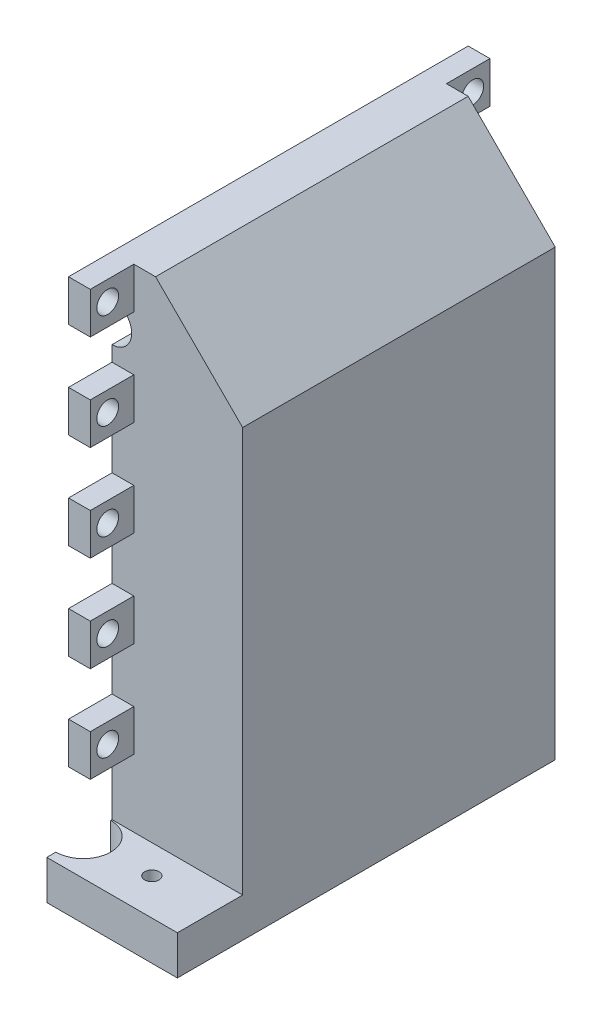
SolidWorks part; units mm, degrees
material "ABS"
ref_plane "Front Plane" through (0, 0, 0) normal (0, 0, 1) x (1, 0, 0)
ref_plane "Top Plane" through (0, 0, 0) normal (0, 1, 0) x (1, 0, 0)
ref_plane "Right Plane" through (0, 0, 0) normal (1, 0, 0) x (0, 0, -1)
sketch "Sketch1" plane through (0, 0, 0) normal (0, 1, 0) x (1, 0, 0)
  line L0 (0, 0) -> (14.605, 0)
  line L1 (21.08, 8.638) -> (48.0208, -18.3028) construction
  line L2 (29.718, 15.113) -> (29.718, 44.323)
  line L3 (21.08, 50.798) -> (48.0208, 77.7388) construction
  line L4 (14.605, 59.436) -> (0, 59.436)
  line L5 (0, 0) -> (0, -25.4)
  line L6 (0, -25.4) -> (38.1, -25.4)
  line L7 (38.1, -25.4) -> (38.1, 84.836)
  line L8 (38.1, 84.836) -> (0, 84.836)
  line L9 (0, 84.836) -> (0, 59.436)
  line L10 (0, 59.436) -> (0.0016, 59.4863)
  arc A0 (14.605, 59.436) -> (29.718, 44.323) centre (48.0208, 77.7388) ccw
  arc A1 (14.605, 0) -> (29.718, 15.113) centre (48.0208, -18.3028) cw
  circle A2 centre (23.622, 6.096) radius 2.54
  circle A3 centre (23.622, 53.34) radius 2.54
  dimension "D9" = 38.1
  dimension "D6" = 38.1
  dimension "D4" = 5.08
  dimension "D11" = 5.08
  dimension "D1" = 29.718
  dimension "D2" = 59.436
  dimension "D3" = 14.605
  dimension "D5" = 29.21
  dimension "D7" = 38.1
  dimension "D8" = 25.4
  dimension "D10" = 25.4
  dimension "D12" = 47.244
extrude "Boss-Extrude1" add sketch "Sketch1" along normal blind 11.43
sketch "Sketch2" plane through (0, 11.43, 0) normal (0, 1, 0) x (1, 0, 0)
  line L0 (38.1, 84.836) -> (0, 84.836) construction
  line L2 (38.1, 84.836) -> (29.718, 84.836)
  line L3 (29.718, 0) -> (29.718, 84.836)
  line L4 (29.718, 15.113) -> (29.718, 44.323) construction
  line L12 (38.1, 84.836) -> (0, 84.836)
  line L13 (0, 84.836) -> (0, 59.436)
  line L14 (0, 59.436) -> (14.605, 59.436)
  line L16 (29.718, 44.323) -> (29.718, 15.113)
  line L18 (14.605, 0) -> (0, 0)
  line L19 (0, 0) -> (0, -25.4)
  line L20 (0, -25.4) -> (38.1, -25.4)
  line L21 (38.1, -25.4) -> (38.1, 84.836)
  line L28 (29.718, 0) -> (0, 0)
  line L29 (0, 0) -> (0, -6.35)
  line L30 (0, -6.35) -> (38.1, -6.35)
  line L31 (38.1, -6.35) -> (38.1, 84.836)
  arc A1 (14.605, 59.436) -> (29.718, 44.323) centre (48.0208, 77.7388) ccw
  arc A3 (29.718, 15.113) -> (14.605, 0) centre (48.0208, -18.3028) ccw
  dimension "D2" = 6.35
  dimension "D1" = 0
extrude "Boss-Extrude2" add sketch "Sketch2" along normal blind 107.95
sketch "Sketch3" plane through (0, 119.38, 0) normal (0, 1, 0) x (1, 0, 0)
  line L0 (38.1, -6.35) -> (38.1, 84.836) construction
  line L1 (0, -6.35) -> (38.1, -6.35)
  line L2 (0, -6.35) -> (0, 84.836)
  line L3 (0, 84.836) -> (38.1, 84.836)
  line L4 (38.1, -6.35) -> (38.1, 84.836)
  line L5 (29.718, 84.836) -> (0, 84.836) construction
  line L6 (0, -6.35) -> (38.1, -6.35) construction
  line L7 (0, 0) -> (0, -6.35) construction
extrude "Boss-Extrude3" add sketch "Sketch3" along normal blind 35.56
sketch "Sketch4" plane through (0, 0, 6.35) normal (0, 0, 1) x (1, 0, 0)
  line L0 (0, 11.43) -> (0, 0) construction
  line L1 (0, 154.94) -> (38.1, 154.94) construction
  circle A0 centre (0, 137.16) radius 5.715
  dimension "D1" = 11.43
  dimension "D2" = 17.78
extrude "Cut-Extrude1" cut sketch "Sketch4" against normal up to next
mirror "Mirror2" [suppressed]
sketch "Sketch5" plane through (0, 0, 6.35) normal (0, 0, 1) x (1, 0, 0)
  line L0 (0, 11.43) -> (0, 0) construction
  line L1 (0, 142.875) -> (6.35, 142.875)
  line L2 (0, 142.875) -> (0, 154.94)
  line L3 (0, 154.94) -> (6.35, 154.94)
  line L4 (6.35, 142.875) -> (6.35, 154.94)
  line L6 (0, 154.94) -> (38.1, 154.94) construction
  dimension "D3" = 6.35
extrude "Boss-Extrude4" add sketch "Sketch5" along normal blind 12.7
hole_wizard "1/4 (0.25) Diameter Hole2" positions "Sketch9" profile "Sketch10" hole size "1/4" standard "ANSI Inch" end condition up to next
sketch "Sketch9" plane through (6.35, 0, 0) normal (1, 0, 0) x (0, 0, -1)
  line L1 (-19.05, 154.94) -> (-6.35, 154.94) construction
  line L2 (-19.05, 142.875) -> (-19.05, 154.94) construction
  point P0 (-13.97, 149.225)
  dimension "D1" = 5.08
  dimension "D2" = 5.715
sketch "Sketch10" plane through (6.35, 149.225, 13.97) normal (0, 1, 0) x (0, 0, -1)
  line L0 (0, 0) -> (0, 6.351)
  line L1 (0, 6.351) -> (3.175, 6.351)
  line L2 (3.175, 6.351) -> (3.175, 0)
  line L5 (3.175, 0) -> (0, 0)
  line L11 (0, -6.35) -> (0, 107.95) construction
  dimension "Thru Hole Dia." = 6.35
  dimension "Thru Hole Depth" = 6.351
pattern_linear "LPattern2" count 5 spacing 27.94 along (0, -1, 0) of "1/4 (0.25) Diameter Hole2", "Boss-Extrude4"
sketch "Sketch13" plane through (0, 0, -84.836) normal (0, 0, -1) x (-1, 0, 0)
  line L0 (-29.718, 11.43) -> (0, 11.43) construction
  line L1 (0, 0) -> (-6.35, 0)
  line L2 (0, 0) -> (0, 11.43)
  line L3 (0, 11.43) -> (-6.35, 11.43)
  line L4 (-6.35, 0) -> (-6.35, 11.43)
  dimension "D1" = 6.35
extrude "Boss-Extrude5" add sketch "Sketch13" along normal blind 12.7
hole_wizard "1/4 (0.25) Diameter Hole3" positions "Sketch14" profile "Sketch15" hole size "1/4" standard "ANSI Inch" end condition up to next
sketch "Sketch14" plane through (6.35, 0, 0) normal (1, 0, 0) x (0, 0, -1)
  line L0 (97.536, 11.43) -> (97.536, 0) construction
  point P0 (92.456, 5.715)
  point P9 (97.536, 5.715)
  dimension "D1" = 5.08
sketch "Sketch15" plane through (6.35, 5.715, -92.456) normal (0, 1, 0) x (0, 0, -1)
  line L0 (0, 0) -> (0, 6.35)
  line L1 (0, 6.35) -> (3.175, 6.35)
  line L2 (3.175, 6.35) -> (3.175, 0)
  line L5 (3.175, 0) -> (0, 0)
  line L11 (0, -6.35) -> (0, 107.95) construction
  dimension "Thru Hole Dia." = 6.35
  dimension "Thru Hole Depth" = 6.35
sketch "Sketch16" plane through (0, 0, -84.836) normal (0, 0, -1) x (-1, 0, 0)
  line L1 (0, 154.94) -> (-6.35, 154.94)
  line L2 (0, 154.94) -> (0, 142.875)
  line L3 (0, 142.875) -> (-6.35, 142.875)
  line L4 (-6.35, 154.94) -> (-6.35, 142.875)
  dimension "D1" = 6.35
extrude "Boss-Extrude6" add sketch "Sketch16" along normal blind 12.7
hole_wizard "1/4 (0.25) Diameter Hole4" positions "Sketch17" profile "Sketch18" hole size "1/4" standard "ANSI Inch" end condition up to next
sketch "Sketch17" plane through (6.35, 0, 0) normal (1, 0, 0) x (0, 0, -1)
  line L0 (97.536, 154.94) -> (97.536, 142.875) construction
  point P0 (92.5156, 148.9075)
  point P5 (97.536, 148.9075)
  dimension "D1" = 5.0204
sketch "Sketch18" plane through (6.35, 148.9075, -92.5156) normal (0, 1, 0) x (0, 0, -1)
  line L0 (0, 0) -> (0, 6.35)
  line L1 (0, 6.35) -> (3.175, 6.35)
  line L2 (3.175, 6.35) -> (3.175, 0)
  line L5 (3.175, 0) -> (0, 0)
  line L11 (0, -6.35) -> (0, 107.95) construction
  dimension "Thru Hole Dia." = 6.35
  dimension "Thru Hole Depth" = 6.35
sketch "Sketch19" plane through (0, 0, -84.836) normal (0, 0, -1) x (-1, 0, 0)
  line L0 (-29.718, 119.38) -> (0, 119.38) construction
  line L1 (0, 131.445) -> (-6.35, 131.445)
  line L2 (0, 131.445) -> (0, 119.38)
  line L3 (0, 119.38) -> (-6.35, 119.38)
  line L4 (-6.35, 131.445) -> (-6.35, 119.38)
  line L5 (-6.35, 154.94) -> (-6.35, 142.875) construction
extrude "Boss-Extrude7" add sketch "Sketch19" along normal up to surface (12.7 mm away) up to face at (3.175, 148.9075, -97.536)
hole_wizard "1/4 (0.25) Diameter Hole5" positions "Sketch20" profile "Sketch21" hole size "1/4" standard "ANSI Inch" end condition up to next
sketch "Sketch20" plane through (6.35, 0, 0) normal (1, 0, 0) x (0, 0, -1)
  line L0 (97.536, 119.38) -> (97.536, 131.445) construction
  point P0 (92.456, 125.4125)
  point P6 (97.536, 125.4125)
  dimension "D1" = 5.08
sketch "Sketch21" plane through (6.35, 125.4125, -92.456) normal (0, 1, 0) x (0, 0, -1)
  line L0 (0, 0) -> (0, 6.35)
  line L1 (0, 6.35) -> (3.175, 6.35)
  line L2 (3.175, 6.35) -> (3.175, 0)
  line L5 (3.175, 0) -> (0, 0)
  line L11 (0, -6.35) -> (0, 107.95) construction
  dimension "Thru Hole Dia." = 6.35
  dimension "Thru Hole Depth" = 6.35
chamfer "Chamfer1" distance 25.4 angle 45 1 edges at (38.1, 154.94, -39.243)
hole_wizard "Tap Drill for M5x0.8 Tap1" positions "Sketch22" profile "Sketch23" hole size "M5x0.8" standard "ANSI Metric" end condition up to next
sketch "Sketch22" plane through (0, 0, 0) normal (0, -1, 0) x (-1, 0, 0)
  line L0 (0, 97.536) -> (0, 59.436) construction
  line L3 (-20, 74.168) -> (-20, -14.732) construction
  line L7 (-38.1, -25.4) -> (-38.1, 84.836) construction
  point P0 (-20, 74.168)
  point P2 (-20, -14.732)
  point P42 (-20, -15.0919)
  point P50 (-38.1, 29.718)
  point P51 (-20, 29.718)
  dimension "D1" = 20
  dimension "D2" = 88.9
sketch "Sketch23" plane through (20, 0, -74.168) normal (1, 0, 0) x (0, 0, -1)
  line L0 (0, 0) -> (0, 11.43)
  line L1 (0, 11.43) -> (2.1, 11.43)
  line L2 (2.1, 11.43) -> (2.1, 0)
  line L5 (2.1, 0) -> (0, 0)
  line L11 (0, -6.35) -> (0, 107.95) construction
  dimension "Thru Hole Dia." = 4.2
  dimension "Thru Hole Depth" = 11.43
sketch "Sketch24" plane through (0, 0, 0) normal (0, -1, 0) x (1, 0, 0)
  line L0 (0, -97.536) -> (0, -59.436) construction
  line L1 (0, 0) -> (0, 25.4) construction
  line L4 (0, -74.168) -> (0, 14.732) construction
  line L5 (38.1, 25.4) -> (38.1, -84.836) construction
  circle A0 centre (0, -74.168) radius 8
  circle A1 centre (0, 14.732) radius 8
  point P8 (0, -29.718)
  point P11 (38.1, -29.718)
  dimension "D1" = 16
  dimension "D2" = 16
  dimension "D3" = 88.9
extrude "Cut-Extrude2" cut sketch "Sketch24" against normal up to next
